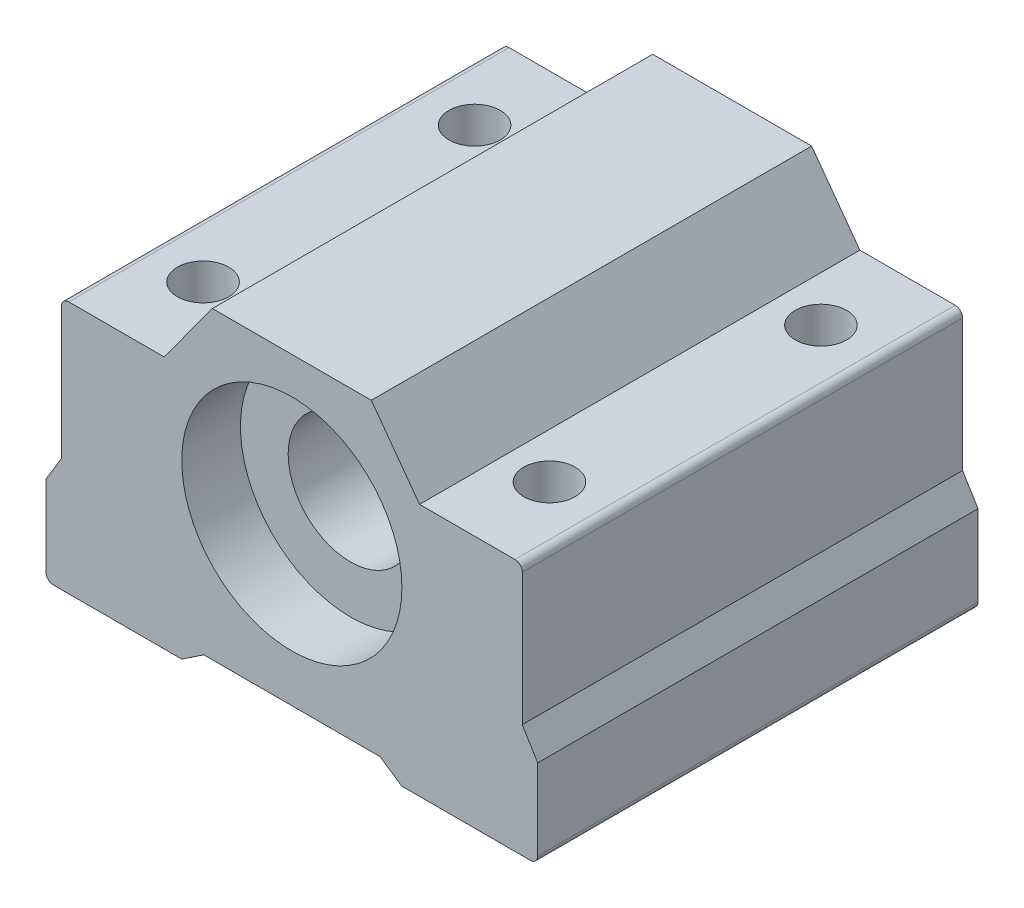
SolidWorks part; units mm, degrees
ref_plane "Alzado" through (0, 0, 0) normal (0, 0, 1) x (1, 0, 0)
ref_plane "Planta" through (0, 0, 0) normal (0, 1, 0) x (1, 0, 0)
ref_plane "Vista lateral" through (0, 0, 0) normal (1, 0, 0) x (0, 0, -1)
sketch "Croquis1" plane through (0, 0, 0) normal (0, 0, 1) x (1, 0, 0)
  line L0 (-15.2, 0) -> (-8.7, 0)
  line L1 (0, 0) -> (0, 4.5) construction
  line L2 (-5.415, 4.5) -> (5.415, 4.5)
  line L3 (5.415, 4.5) -> (8.7, 0)
  line L4 (-5.415, 4.5) -> (-8.7, 0)
  line L5 (-6, -16.23) -> (6, -16.23)
  line L6 (-6, -16.23) -> (-7.5, -17.23)
  line L7 (7.5, -17.23) -> (16.25, -17.23)
  line L8 (6, -16.23) -> (7.5, -17.23)
  line L9 (-7.5, -17.23) -> (-16.25, -17.23)
  line L10 (16.75, -16.73) -> (16.75, -11.23)
  line L11 (15.7, -0.5) -> (15.7, -9.5)
  line L12 (15.7, -9.5) -> (16.75, -11.23)
  line L13 (-16.75, -16.73) -> (-16.75, -11.23)
  line L14 (-15.7, -9.5) -> (-16.75, -11.23)
  line L15 (-15.7, -0.5) -> (-15.7, -9.5)
  line L16 (8.7, 0) -> (15.2, 0)
  arc A0 (15.2, 0) -> (15.7, -0.5) centre (15.2, -0.5) cw
  arc A1 (-15.2, 0) -> (-15.7, -0.5) centre (-15.2, -0.5) ccw
  arc A2 (16.25, -17.23) -> (16.75, -16.73) centre (16.25, -16.73) ccw
  arc A3 (-16.25, -17.23) -> (-16.75, -16.73) centre (-16.25, -16.73) cw
  point P4 (0, 0)
  point P5 (8.7, 0)
  point P9 (0, 4.5)
  point P12 (0, -16.23)
  point P16 (0, -16.23)
  point P18 (7.5, -17.23)
  point P25 (15.7, 0)
  point P32 (16.75, -17.23)
  point P35 (-16.75, -17.23)
  point P36 (0, 0)
  dimension "D10" = 0.5
  dimension "D11" = 0.5
  dimension "D12" = 0.5
  dimension "D1" = 30.9
  dimension "D2" = 4.5
  dimension "D3" = 10.83
  dimension "D4" = 7
  dimension "D5" = 20.73
  dimension "D6" = 12
  dimension "D7" = 6
  dimension "D8" = 9.5
  dimension "D9" = 9.25
extrude "Saliente-Extruir1" add sketch "Croquis1" along normal blind 30
sketch "Croquis2" plane through (0, 0, 0) normal (0, 0, 1) x (1, 0, 0)
  line L0 (5.415, 4.5) -> (-5.415, 4.5) construction
  line L1 (15.7, -9.5) -> (15.7, -0.5) construction
  circle A0 centre (0, -5.5) radius 7.5
  point P0 (-3.7417, 1)
  point P3 (7.7, -6.5008)
  point P8 (0, 0)
  dimension "D4" = 15
  dimension "D1" = 3.5
  dimension "D2" = 8
  dimension "D3" = 10
  dimension "D5" = 0
extrude "Cortar-Extruir1" cut sketch "Croquis2" along normal blind 4
ref_plane "Plano1" through (0, 0, 15) normal (0, 0, -1) x (-1, 0, 0)
mirror "Simetría1" about plane through (0, 0, 15) normal (0, 0, -1) of "Cortar-Extruir1"
sketch "Croquis3" plane through (0, 0, 15) normal (0, 0, -1) x (-1, 0, 0)
  circle A4 centre (0, -5.5) radius 4.25
  circle A5 centre (0, -5.5) radius 7.5 construction
  dimension "D1" = 8.5
extrude "Cortar-Extruir2" cut sketch "Croquis3" along normal through all both and the other way through all
sketch "Croquis5" plane through (0, -17.23, 0) normal (0, -1, 0) x (1, 0, 0)
  line L0 (0, 30) -> (0, 0) construction
  line L1 (-6, 30) -> (6, 30) construction
  line L2 (-16.25, 30) -> (-7.5, 30) construction
  line L5 (-16.25, 30) -> (-16.25, 0) construction
  line L6 (9.7084, 15) -> (-15.1216, 15)
  line L7 (-11.9515, 15) -> (11.9515, 15) construction
  circle A0 centre (-11.8, 24.25) radius 1.75
  circle A1 centre (11.8, 24.25) radius 1.75
  circle A2 centre (11.8, 5.75) radius 1.75
  circle A3 centre (-11.8, 5.75) radius 1.75
  dimension "D1" = 3.5
  dimension "D3" = 4.45
  dimension "D2" = 5.75
extrude "Cortar-Extruir3" cut sketch "Croquis5" against normal through all both and the other way through all contours A0 | A1 | A2 | A3
chamfer "Chaflán1" distance 0.5 angle 45 4 edges at (-11.8, -17.23, 26) (-11.8, -17.23, 7.5) (11.8, -17.23, 7.5) (11.8, -17.23, 26)
